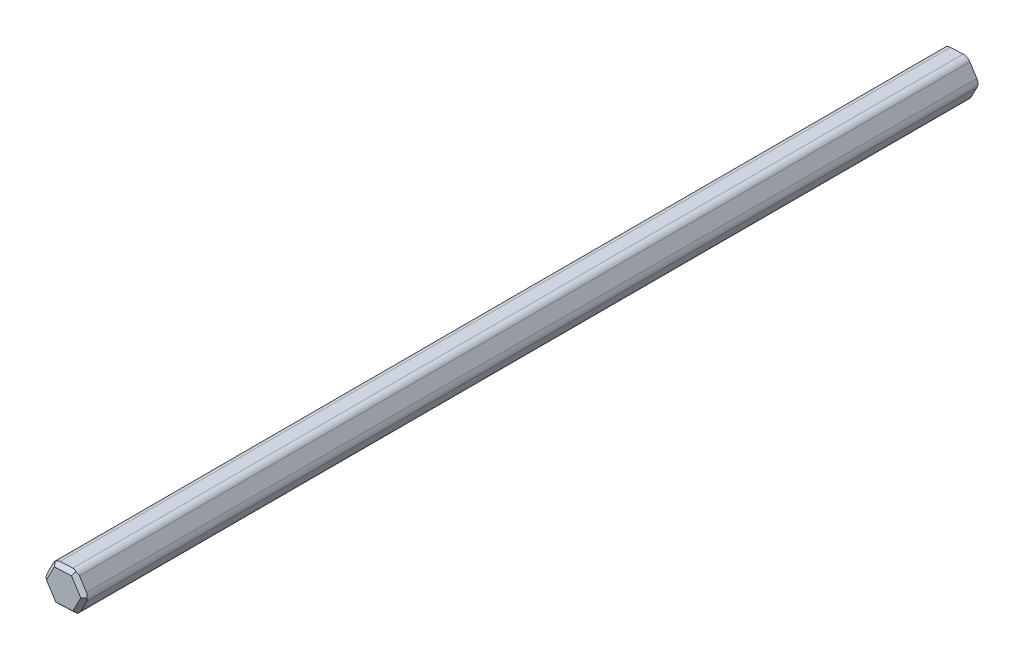
SolidWorks part; units mm, degrees
ref_plane "Front Plane" through (0, 0, 0) normal (0, 0, 1) x (1, 0, 0)
ref_plane "Top Plane" through (0, 0, 0) normal (0, 1, 0) x (1, 0, 0)
ref_plane "Right Plane" through (0, 0, 0) normal (1, 0, 0) x (0, 0, -1)
sketch "Sketch1" plane through (0, 0, 0) normal (0, 0, 1) x (1, 0, 0)
  line L1 (-0.7914, 1.2346) -> (-1.4649, -0.068)
  line L2 (-1.4649, -0.068) -> (-0.6735, -1.3027)
  line L3 (-0.6735, -1.3027) -> (0.7914, -1.2346)
  line L4 (0.7914, -1.2346) -> (1.4649, 0.068)
  line L5 (1.4649, 0.068) -> (0.6735, 1.3027)
  line L6 (0.6735, 1.3027) -> (-0.7914, 1.2346)
  circle A0 centre (0, 0) radius 1.27 construction
extrude "Boss-Extrude1" add sketch "Sketch1" along normal blind 60.96
chamfer "Chamfer1" distance 0.254 angle 45 6 edges at (-1.0692, -0.6853, 60.96) (0.0589, -1.2686, 60.96) (1.1281, -0.5833, 60.96) (1.0692, 0.6853, 60.96) (-0.0589, 1.2686, 60.96) (-1.1281, 0.5833, 60.96)
fillet "Fillet1" radius 0.508 6 edges at (-0.7914, 1.2346, 30.353) (0.7914, -1.2346, 30.353) (-1.4649, -0.068, 30.353) (-0.6735, -1.3027, 30.353) (0.6735, 1.3027, 30.353) (1.4649, 0.068, 30.353)
